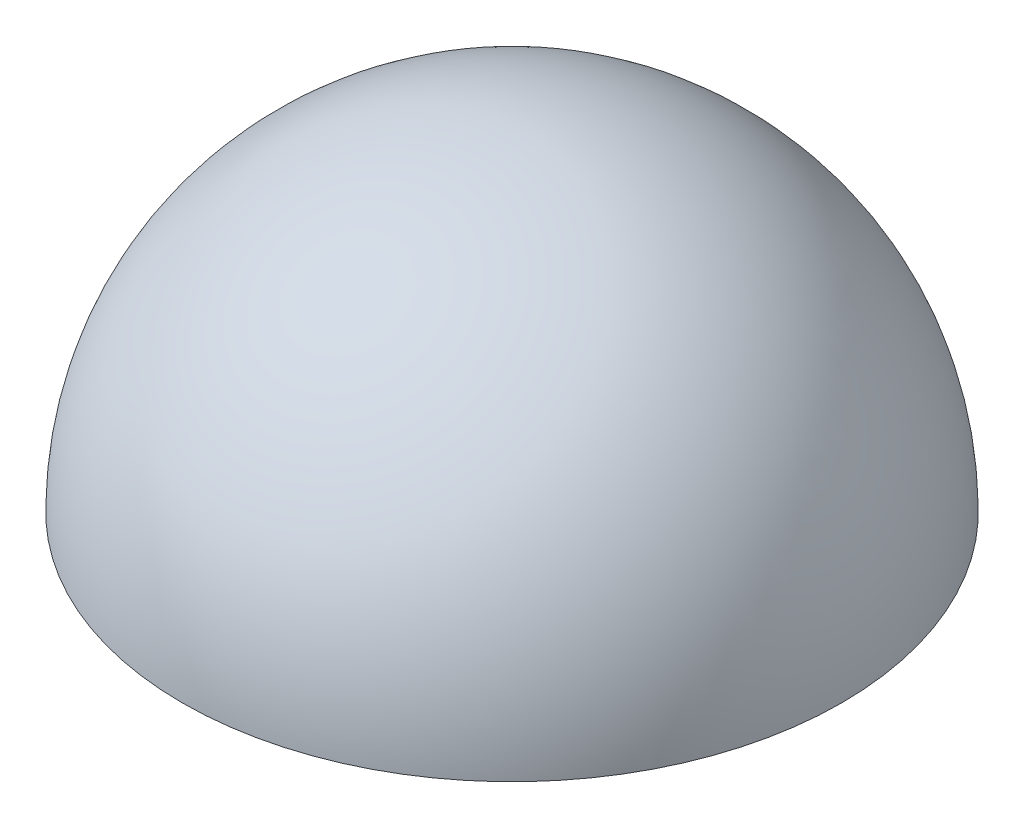
SolidWorks part; units mm, degrees
ref_plane "Front Plane" through (0, 0, 0) normal (0, 0, 1) x (1, 0, 0)
ref_plane "Top Plane" through (0, 0, 0) normal (0, 1, 0) x (1, 0, 0)
ref_plane "Right Plane" through (0, 0, 0) normal (1, 0, 0) x (0, 0, -1)
sketch "Sketch1" plane through (0, 0, 0) normal (0, 0, 1) x (1, 0, 0)
  line L0 (0, 3.2) -> (0, 3.8)
  line L1 (3.8, 0) -> (3.2, 0)
  arc A0 (3.2, 0) -> (0, 3.2) centre (0, 0) ccw
  arc A1 (3.8, 0) -> (0, 3.8) centre (0, 0) ccw
  dimension "D1" = 3.2
  dimension "D2" = 3.8
sketch "Sketch2" plane through (0, 0, 0) normal (0, 0, 1) x (1, 0, 0)
  line L0 (0, 3.1) -> (0, 0)
  line L1 (0, 0) -> (3.1, 0)
  arc A0 (3.1, 0) -> (0, 3.1) centre (0, 0) ccw
  dimension "D1" = 3.1
  dimension "D2" = 3.1
revolve "Revolve1" add sketch "Sketch1" angle 360 about L0
revolve "Revolve2" add sketch "Sketch2" angle 360 about L0
